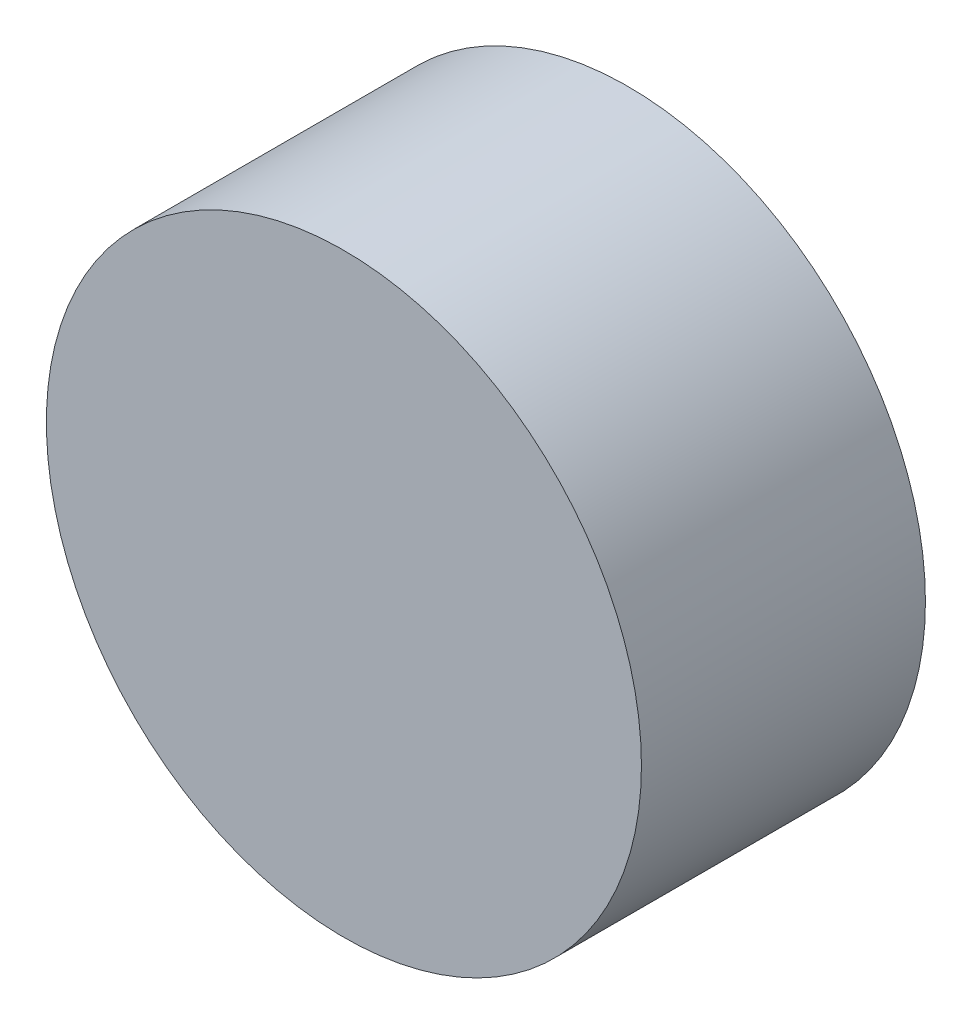
SolidWorks part; units mm, degrees
ref_plane "Front Plane" through (0, 0, 0) normal (0, 0, 1) x (1, 0, 0)
ref_plane "Top Plane" through (0, 0, 0) normal (0, 1, 0) x (1, 0, 0)
ref_plane "Right Plane" through (0, 0, 0) normal (1, 0, 0) x (0, 0, -1)
sketch "Sketch1" plane through (0, 0, 0) normal (0, 0, 1) x (1, 0, 0)
  circle A0 centre (0, 0) radius 34.925
  dimension "D1" = 69.85
extrude "Boss-Extrude1" add sketch "Sketch1" along normal blind 33.3375
